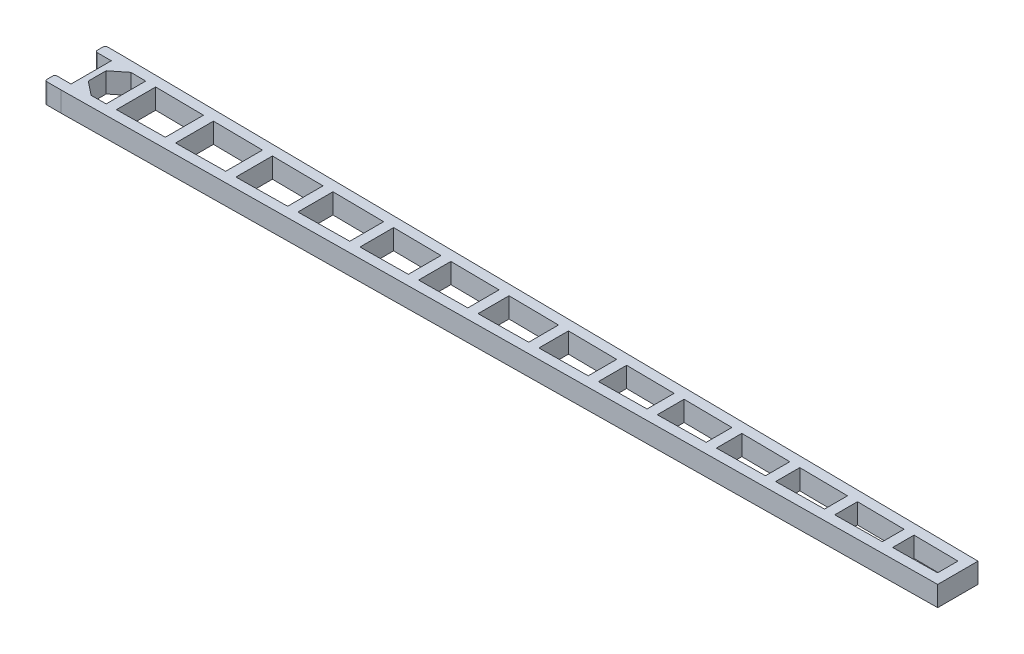
SolidWorks part; units mm, degrees
ref_plane "Front Plane" through (0, 0, 0) normal (0, 0, 1) x (1, 0, 0)
ref_plane "Top Plane" through (0, 0, 0) normal (0, 1, 0) x (1, 0, 0)
ref_plane "Right Plane" through (0, 0, 0) normal (1, 0, 0) x (0, 0, -1)
sketch "Croquis1" plane through (0, 0, 0) normal (0, 1, 0) x (1, 0, 0)
  line L0 (347.7685, -7.5192) -> (347.7685, 12.4808)
  line L1 (-82.2315, 12.4808) -> (-82.2315, -7.5192)
  line L2 (347.7685, 12.4808) -> (-82.2315, 17.4808)
  line L3 (-82.2315, -12.5192) -> (347.7685, -7.5192)
  line L4 (347.7685, 2.4808) -> (-90.9091, 2.4808) construction
  line L5 (-35.9703, -6.9813) -> (-35.9703, 11.9428)
  line L6 (-59.9703, 12.2219) -> (-59.9703, -7.2604)
  line L7 (-35.9703, 11.9428) -> (-59.9703, 12.2219)
  line L8 (-59.9703, -7.2604) -> (-35.9703, -6.9813)
  line L9 (-35.9703, 2.4808) -> (-69.1923, 2.4808) construction
  line L18 (-56.9599, 12.1869) -> (-56.9599, 17.1869) construction
  line L23 (-6.3668, -6.6371) -> (-6.3668, 11.5986)
  line L24 (-30.9703, 11.8847) -> (-30.9703, -6.9232)
  line L25 (-6.3668, 11.5986) -> (-30.9703, 11.8847)
  line L26 (-30.9703, -6.9232) -> (-6.3668, -6.6371)
  line L27 (-26.319, 11.8306) -> (-26.319, 16.8306) construction
  line L28 (-25.4286, -6.8587) -> (-25.4286, -11.8587) construction
  line L29 (24.0325, -6.2836) -> (24.0325, 11.2451)
  line L30 (-1.3668, 11.5405) -> (-1.3668, -6.579)
  line L31 (24.0325, 11.2451) -> (-1.3668, 11.5405)
  line L32 (-1.3668, -6.579) -> (24.0325, -6.2836)
  line L33 (4.6431, 11.4706) -> (4.6431, 16.4706) construction
  line L34 (5.5251, -6.4988) -> (5.5251, -11.4988) construction
  line L35 (54.4717, -5.9297) -> (54.4717, 10.8912)
  line L36 (29.0325, 11.187) -> (29.0325, -6.2255)
  line L37 (54.4717, 10.8912) -> (29.0325, 11.187)
  line L38 (29.0325, -6.2255) -> (54.4717, -5.9297)
  line L39 (34.3658, 11.125) -> (34.3658, 16.125) construction
  line L40 (35.2726, -6.1529) -> (35.2726, -11.1529) construction
  line L41 (83.2091, -5.5955) -> (83.2091, 10.557)
  line L42 (59.4717, 10.833) -> (59.4717, -5.8715)
  line L43 (83.2091, 10.557) -> (59.4717, 10.833)
  line L44 (59.4717, -5.8715) -> (83.2091, -5.5955)
  line L45 (64.1961, 10.7781) -> (64.1961, 15.7781) construction
  line L46 (65.111, -5.806) -> (65.111, -10.806) construction
  line L47 (112.3956, -5.2561) -> (112.3956, 10.2177)
  line L48 (88.2091, 10.4989) -> (88.2091, -5.5374)
  line L49 (112.3956, 10.2177) -> (88.2091, 10.4989)
  line L50 (88.2091, -5.5374) -> (112.3956, -5.2561)
  line L51 (93.1144, 10.4419) -> (93.1144, 15.4419) construction
  line L52 (94.0371, -5.4696) -> (94.0371, -10.4696) construction
  line L53 (142.2465, -4.909) -> (142.2465, 9.8706)
  line L54 (117.3956, 10.1595) -> (117.3956, -5.198)
  line L55 (142.2465, 9.8706) -> (117.3956, 10.1595)
  line L56 (117.3956, -5.198) -> (142.2465, -4.909)
  line L57 (122.5609, 10.0995) -> (122.5609, 15.0995) construction
  line L58 (123.8881, -5.1225) -> (123.8881, -10.1225) construction
  line L59 (171.4378, -4.5696) -> (171.4378, 9.5311)
  line L60 (147.2465, 9.8124) -> (147.2465, -4.8509)
  line L61 (171.4378, 9.5311) -> (147.2465, 9.8124)
  line L62 (147.2465, -4.8509) -> (171.4378, -4.5696)
  line L63 (152.4745, 9.7516) -> (152.4745, 14.7516) construction
  line L64 (153.3811, -4.7796) -> (153.3811, -9.7796) construction
  line L65 (200.2884, -4.2341) -> (200.2884, 9.1956)
  line L66 (176.4378, 9.473) -> (176.4378, -4.5115)
  line L67 (200.2884, 9.1956) -> (176.4378, 9.473)
  line L68 (176.4378, -4.5115) -> (200.2884, -4.2341)
  line L69 (181.2934, 9.4165) -> (181.2934, 14.4165) construction
  line L70 (182.1923, -4.4445) -> (182.1923, -9.4445) construction
  line L71 (229.2883, -3.8969) -> (229.2883, 8.8584)
  line L72 (205.2884, 9.1375) -> (205.2884, -4.176)
  line L73 (229.2883, 8.8584) -> (205.2884, 9.1375)
  line L74 (205.2884, -4.176) -> (229.2883, -3.8969)
  line L75 (210.1756, 9.0807) -> (210.1756, 14.0807) construction
  line L76 (211.0667, -4.1088) -> (211.0667, -9.1088) construction
  line L77 (258.3576, -3.5589) -> (258.3576, 8.5204)
  line L78 (234.2883, 8.8003) -> (234.2883, -3.8388)
  line L79 (258.3576, 8.5204) -> (234.2883, 8.8003)
  line L80 (234.2883, -3.8388) -> (258.3576, -3.5589)
  line L81 (239.2933, 8.7421) -> (239.2933, 13.7421) construction
  line L82 (240.1765, -3.7703) -> (240.1765, -8.7703) construction
  line L83 (287.3259, -3.2221) -> (287.3259, 8.1836)
  line L84 (263.3576, 8.4623) -> (263.3576, -3.5008)
  line L85 (287.3259, 8.1836) -> (263.3576, 8.4623)
  line L86 (263.3576, -3.5008) -> (287.3259, -3.2221)
  line L87 (268.3142, 8.4046) -> (268.3142, 13.4046) construction
  line L88 (269.1895, -3.4329) -> (269.1895, -8.4329) construction
  line L89 (315.7096, -2.892) -> (315.7096, 7.8535)
  line L90 (292.3259, 8.1254) -> (292.3259, -3.1639)
  line L91 (315.7096, 7.8535) -> (292.3259, 8.1254)
  line L92 (292.3259, -3.1639) -> (315.7096, -2.892)
  line L93 (297.2299, 8.0684) -> (297.2299, 13.0684) construction
  line L94 (298.0974, -3.0968) -> (298.0974, -8.0968) construction
  line L95 (342.7685, -2.5774) -> (342.7685, 7.5389)
  line L96 (320.7096, 7.7954) -> (320.7096, -2.8339)
  line L97 (342.7685, 7.5389) -> (320.7096, 7.7954)
  line L98 (320.7096, -2.8339) -> (342.7685, -2.5774)
  line L99 (325.0814, 7.7446) -> (325.0814, 12.7446) construction
  line L100 (325.9414, -2.773) -> (325.9414, -7.773) construction
  line L101 (-64.9703, -7.3185) -> (-64.9703, 12.28)
  line L103 (-64.9703, 12.28) -> (-72.3872, 12.3663)
  line L104 (-72.3872, -7.4048) -> (-64.9703, -7.3185)
  line L105 (-67.4935, -7.3479) -> (-67.4935, -12.3479) construction
  line L106 (-70.6886, 12.3465) -> (-70.6886, 17.3465) construction
  line L107 (-79.2315, 6.9107) -> (-79.2315, -1.9492)
  line L108 (-79.2315, 6.9107) -> (-72.3872, 12.3663)
  line L109 (-79.2315, -1.9492) -> (-72.3872, -7.4048)
  line L111 (-82.2315, -12.5192) -> (-89.2315, -12.5192)
  line L113 (-82.2315, -7.5192) -> (-89.2315, -7.5192)
  line L114 (-90.2315, -11.5192) -> (-90.2315, -8.5192)
  line L115 (-82.2315, 17.4808) -> (-89.2315, 17.4808)
  line L117 (-82.2315, 12.4808) -> (-89.2315, 12.4808)
  line L118 (-90.2315, 16.4808) -> (-90.2315, 13.4808)
  arc A0 (-90.2315, 16.4808) -> (-89.2315, 17.4808) centre (-89.2315, 16.4808) cw
  arc A1 (-90.2315, 13.4808) -> (-89.2315, 12.4808) centre (-89.2315, 13.4808) ccw
  arc A2 (-90.2315, -8.5192) -> (-89.2315, -7.5192) centre (-89.2315, -8.5192) cw
  arc A3 (-89.2315, -12.5192) -> (-90.2315, -11.5192) centre (-89.2315, -11.5192) cw
  point P3 (347.7685, 2.4808)
  point P6 (-82.2315, 2.4808)
  point P13 (-35.9703, 2.4808)
  point P16 (-59.9703, 2.4808)
  point P23 (-6.3668, 2.4808)
  point P25 (-32.6456, 2.3239)
  point P27 (-30.9703, 2.4808)
  point P34 (24.0325, 2.4808)
  point P36 (-1.6814, 2.1462)
  point P38 (-1.3668, 2.4808)
  point P44 (54.4717, 2.4808)
  point P46 (28.0724, 1.5827)
  point P48 (29.0325, 2.4808)
  point P57 (83.2091, 2.4808)
  point P59 (58.0145, 2.4528)
  point P61 (59.4717, 2.4808)
  point P66 (112.3956, 2.4808)
  point P69 (88.2091, 2.4808)
  point P76 (142.2465, 2.4808)
  point P79 (117.3956, 2.4808)
  point P86 (171.4378, 2.4808)
  point P89 (147.2465, 2.4808)
  point P96 (200.2884, 2.4808)
  point P99 (176.4378, 2.4808)
  point P106 (229.2883, 2.4808)
  point P109 (205.2884, 2.4808)
  point P117 (-79.2315, 2.4808)
  point P123 (258.3576, 2.4808)
  point P126 (234.2883, 2.4808)
  point P133 (287.3259, 2.4808)
  point P136 (263.3576, 2.4808)
  point P143 (315.7096, 2.4808)
  point P146 (292.3259, 2.4808)
  point P153 (342.7685, 2.4808)
  point P156 (320.7096, 2.4808)
  point P165 (-90.2315, 17.4808)
  point P170 (-64.9703, 2.4808)
  point P173 (-72.3874, 2.4808)
  point P174 (-90.2315, 12.4808)
  point P179 (-90.2315, -7.5192)
  point P182 (-90.2315, -12.5192)
  dimension "D54" = 1
  dimension "D1" = 20
  dimension "D2" = 30
  dimension "D3" = 430
  dimension "D4" = 5
  dimension "D5" = 5
  dimension "D6" = 24
  dimension "D7" = 5
  dimension "D8" = 5
  dimension "D9" = 5
  dimension "D10" = 5
  dimension "D11" = 5
  dimension "D12" = 5
  dimension "D13" = 5
  dimension "D14" = 5
  dimension "D15" = 5
  dimension "D16" = 5
  dimension "D17" = 5
  dimension "D18" = 5
  dimension "D19" = 5
  dimension "D20" = 5
  dimension "D21" = 5
  dimension "D22" = 5
  dimension "D23" = 5
  dimension "D24" = 5
  dimension "D25" = 5
  dimension "D26" = 5
  dimension "D27" = 5
  dimension "D28" = 5
  dimension "D29" = 5
  dimension "D30" = 5
  dimension "D31" = 5
  dimension "D32" = 5
  dimension "D33" = 5
  dimension "D34" = 5
  dimension "D35" = 5
  dimension "D36" = 5
  dimension "D37" = 5
  dimension "D38" = 5
  dimension "D39" = 5
  dimension "D40" = 5
  dimension "D41" = 5
  dimension "D42" = 5
  dimension "D43" = 5
  dimension "D44" = 5
  dimension "D45" = 5
  dimension "D46" = 5
  dimension "D47" = 5
  dimension "D48" = 5
  dimension "D49" = 3
  dimension "D50" = 8
  dimension "D51" = 8
  dimension "D52" = 5
  dimension "D53" = 5
extrude "Saliente-Extruir2" add sketch "Croquis1" along normal blind 10
scale "Escala1" bodies to scale 108 scale about centroid uniform scaling yes scale factor 0.5
